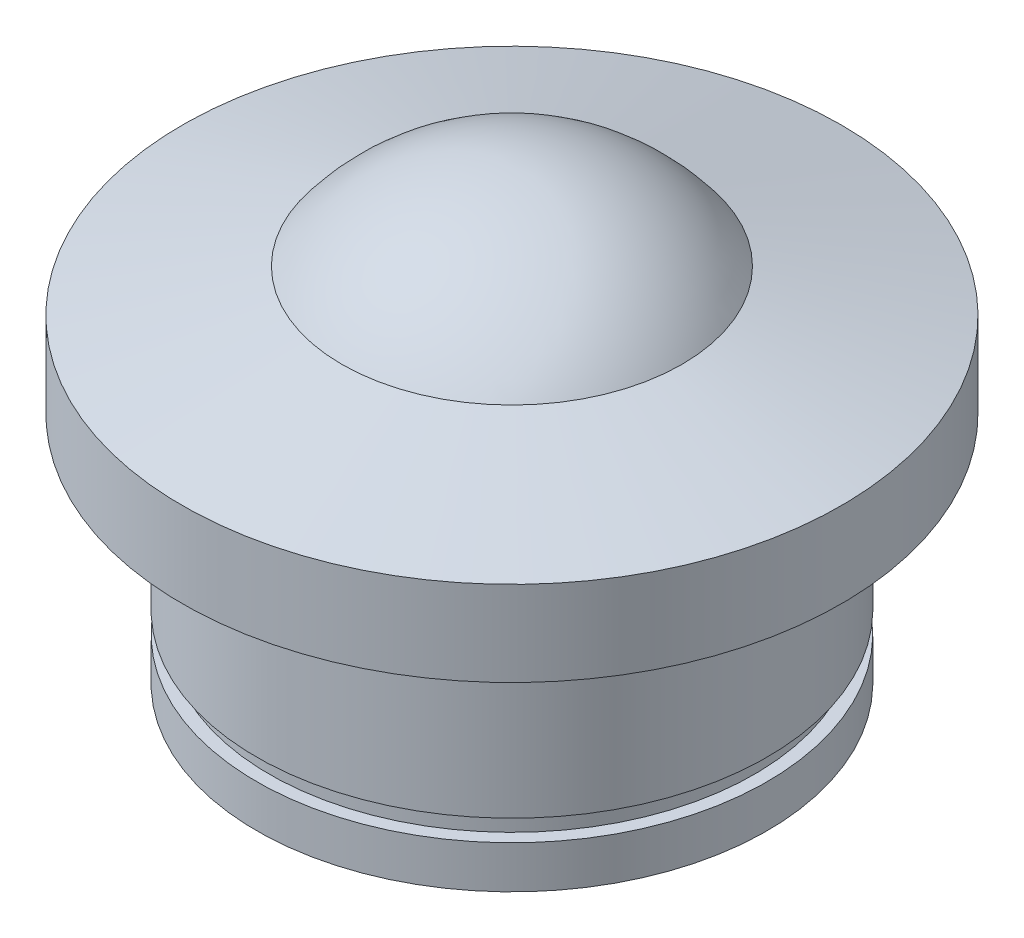
SolidWorks part; units mm, degrees
ref_plane "Plan de face" through (0, 0, 0) normal (0, 0, 1) x (1, 0, 0)
ref_plane "Plan de dessus" through (0, 0, 0) normal (0, 1, 0) x (1, 0, 0)
ref_plane "Plan de droite" through (0, 0, 0) normal (1, 0, 0) x (0, 0, -1)
sketch "Esquisse1" plane through (0, 0, 0) normal (0, 0, 1) x (1, 0, 0)
  line L0 (0, 0) -> (12, 0)
  line L1 (12, 0) -> (12, 2)
  line L2 (12, 2) -> (11.4, 2)
  line L3 (11.4, 2) -> (11.4, 3)
  line L4 (11.4, 3) -> (12, 3)
  line L5 (12, 3) -> (12, 11)
  line L6 (12, 11) -> (15.5, 11)
  line L7 (15.5, 11) -> (15.5, 15)
  line L8 (15.5, 15) -> (8, 17)
  line L9 (0, 0) -> (0, 21)
  arc A0 (8, 17) -> (0, 21) centre (0, 11) ccw
  dimension "D1" = 12
  dimension "D2" = 21
  dimension "D3" = 1
  dimension "D4" = 0.6
  dimension "D5" = 15.5
  dimension "D6" = 2
  dimension "D7" = 2
  dimension "D8" = 4
  dimension "D9" = 17
  dimension "D10" = 8
revolve "Révolution1" add sketch "Esquisse1" angle 360 about L9
